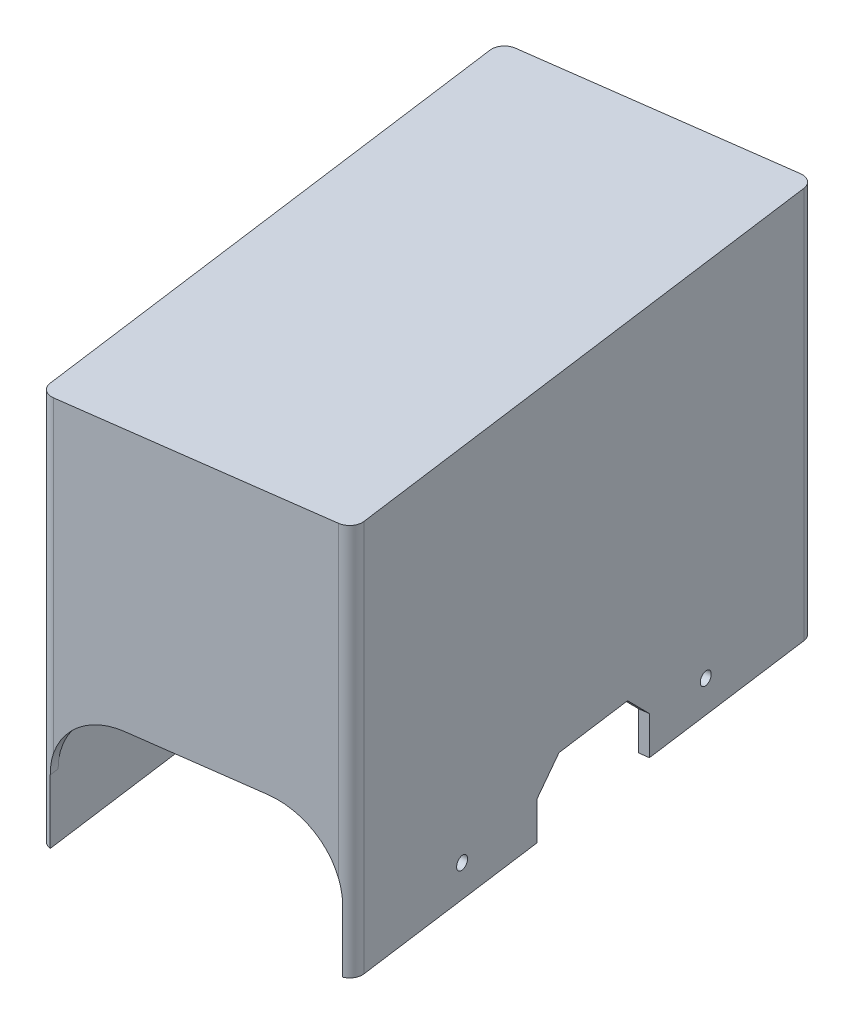
SolidWorks part; units mm, degrees
ref_plane "Front Plane" through (0, 0, 0) normal (0, 0, 1) x (1, 0, 0)
ref_plane "Top Plane" through (0, 0, 0) normal (0, 1, 0) x (1, 0, 0)
ref_plane "Right Plane" through (0, 0, 0) normal (1, 0, 0) x (0, 0, -1)
sketch "Sketch1" plane through (0, 0, 0) normal (0, 1, 0) x (1, 0, 0)
  line L0 (-23.9962, 36.1694) -> (16.4384, 41.6181)
  line L1 (-13.1086, -44.6269) -> (27.3259, -39.1783)
  line L2 (-25.6831, 37.4557) -> (17.7246, 43.305)
  line L3 (29.0128, -40.4645) -> (17.7246, 43.305)
  line L4 (-14.3948, -46.3138) -> (29.0128, -40.4645)
  line L5 (-14.3948, -46.3138) -> (-25.6831, 37.4557)
  line L8 (27.3259, -39.1783) -> (16.4384, 41.6181)
  line L9 (-13.1086, -44.6269) -> (-23.9962, 36.1694)
  dimension "D1" = 1.5
extrude "Boss-Extrude1" add sketch "Sketch1" along normal blind 60
sketch "Sketch2" plane through (0, 60, 0) normal (0, 1, 0) x (1, 0, 0)
  line L4 (-25.6831, 37.4557) -> (-14.3948, -46.3138)
  line L5 (-14.3948, -46.3138) -> (29.0128, -40.4645)
  line L6 (29.0128, -40.4645) -> (17.7246, 43.305)
  line L7 (17.7246, 43.305) -> (-25.6831, 37.4557)
  line L8 (-25.6831, 37.4557) -> (-14.3948, -46.3138)
  line L9 (-14.3948, -46.3138) -> (29.0128, -40.4645)
  line L10 (29.0128, -40.4645) -> (17.7246, 43.305)
  line L11 (17.7246, 43.305) -> (-25.6831, 37.4557)
  dimension "D1" = 0
extrude "Boss-Extrude2" add sketch "Sketch2" along normal blind 1.5
sketch "Sketch3" plane through (5.8729, 0, 43.5827) normal (0.1335, 0, 0.991) x (0.991, 0, -0.1335)
  line L0 (21.4491, 10) -> (21.4491, 0)
  line L1 (-18.5509, 0) -> (-18.5509, 10)
  line L2 (-8.5509, 20) -> (11.4491, 20)
  line L3 (-18.9509, 0) -> (21.8491, 0) construction
  line L4 (-18.9509, 0) -> (21.8491, 0)
  line L5 (-18.5509, 0) -> (21.4491, 0) construction
  line L6 (21.4491, 0) -> (1.4491, 0) construction
  line L8 (-18.9509, -0.4) -> (21.8491, -0.4)
  line L9 (-18.9509, -0.4) -> (-18.9509, 10)
  line L10 (-8.5509, 20.4) -> (11.4491, 20.4)
  line L11 (21.8491, 10) -> (21.8491, -0.4)
  line L12 (-18.9509, -0.4) -> (21.8491, -0.4)
  arc A0 (-8.5509, 20) -> (-18.5509, 10) centre (-8.5509, 10) ccw
  arc A1 (21.4491, 10) -> (11.4491, 20) centre (11.4491, 10) ccw
  arc A2 (-8.5509, 20.4) -> (-18.9509, 10) centre (-8.5509, 10) ccw
  arc A3 (21.8491, 10) -> (11.4491, 20.4) centre (11.4491, 10) ccw
  point P8 (23.3491, 0)
  point P12 (1.4491, 0)
  line M6 (-20.4509, 0) -> (23.3491, 0)
  dimension "D1" = 0.4
extrude "Cut-Extrude1" cut sketch "Sketch3" against normal blind 122.5 contours L0 A1 L2 A0 L1 M6 | L11 A3 L10 A2 L9 L1 A0 L2 A1 L0 M6
fillet "Fillet1" radius 2 4 edges at (17.7246, 30.75, -43.305) (-25.6831, 30.75, -37.4557) (-14.3948, 30.75, 46.3138) (29.0128, 30.75, 40.4645)
sketch "Sketch4" plane through (23.1399, 0, -3.1182) normal (0.991, 0, -0.1335) x (-0.1335, 0, -0.991)
  line L0 (-41.9766, 0) -> (38.55, 0) construction
  line L1 (-1.7133, 0) -> (-1.7133, 10) construction
  line L2 (-1.7133, 5) -> (20.5867, 5) construction
  line L3 (-1.7133, 5) -> (-24.0133, 5) construction
  circle A0 centre (-24.0133, 5) radius 1
  circle A1 centre (20.5867, 5) radius 1
  point P0 (-1.7133, 0)
  dimension "D4" = 2
  dimension "D5" = 2
  dimension "D1" = 10
  dimension "D2" = 22.3
  dimension "D3" = 22.3
extrude "Cut-Extrude2" cut sketch "Sketch4" against normal blind 122.5
sketch "Sketch5" plane through (-20.2677, 0, 2.7311) normal (-0.991, 0, 0.1335) x (0.1335, 0, 0.991)
  line L0 (-10.2761, 0) -> (10.2761, 0)
  line L1 (-10.2761, 10) -> (10.2761, 10)
  line L2 (-10.2761, 10) -> (-10.2761, 0)
  line L4 (10.2761, 10) -> (10.2761, 0)
  line L5 (0, 0) -> (0, 10) construction
  line L6 (-10.2761, 0) -> (10.2761, 0) construction
  point P0 (0, 0)
  dimension "D1" = 10
extrude "Cut-Extrude3" cut sketch "Sketch5" against normal blind 66.5
chamfer "Chamfer2" distance 4 angle 45 4 edges at (-18.1521, 10, 12.815) (23.769, 10, 7.166) (21.0243, 10, -13.2021) (-20.8968, 10, -7.5531)
